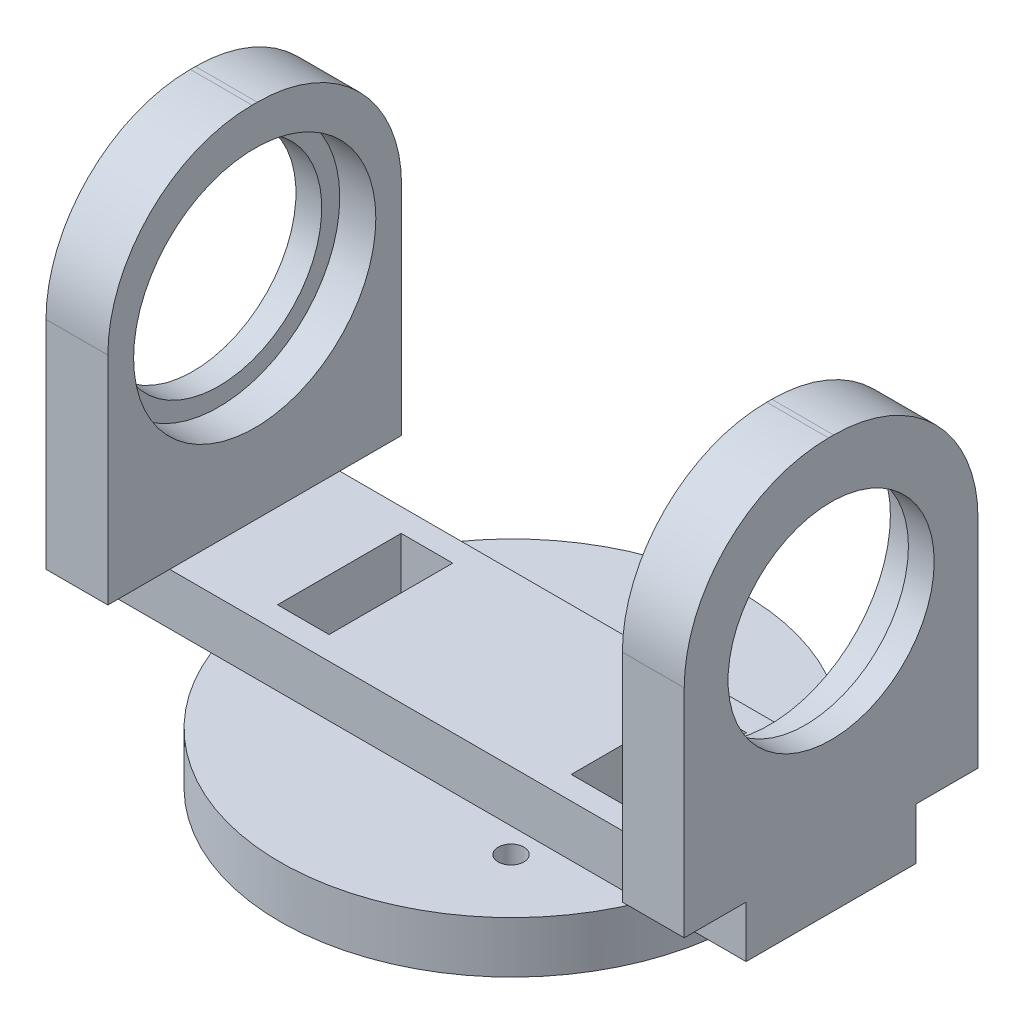
SolidWorks part; units mm, degrees
ref_plane "Front Plane" through (0, 0, 0) normal (0, 0, 1) x (1, 0, 0)
ref_plane "Top Plane" through (0, 0, 0) normal (0, 1, 0) x (1, 0, 0)
ref_plane "Right Plane" through (0, 0, 0) normal (1, 0, 0) x (0, 0, -1)
sketch "Sketch1" plane through (0, 0, 0) normal (0, 1, 0) x (1, 0, 0)
  line L1 (-61.92, 16.5) -> (61.92, 16.5)
  line L2 (-61.92, 16.5) -> (-61.92, -16.5)
  line L3 (-61.92, -16.5) -> (61.92, -16.5)
  line L4 (61.92, 16.5) -> (61.92, -16.5)
  point P4 (-61.92, 0)
  point P6 (0, 16.5)
  dimension "D1" = 33
  dimension "D2" = 123.84
extrude "Boss-Extrude1" add sketch "Sketch1" along normal blind 10 contours L1 L4 L3 L2
sketch "Sketch2" plane through (0, 10, 0) normal (0, 1, 0) x (1, 0, 0)
  line L1 (-61.92, 28.5) -> (-49.92, 28.5)
  line L2 (-61.92, 28.5) -> (-61.92, -28.5)
  line L3 (-61.92, -28.5) -> (-49.92, -28.5)
  line L4 (-49.92, 28.5) -> (-49.92, -28.5)
  line L5 (-23.5, 7.472) -> (-23.5, -3.0599) construction
  line L10 (-61.92, 16.5) -> (-61.92, -16.5) construction
  line L11 (0, 0) -> (0, 32.5393) construction
  line L12 (49.92, 28.5) -> (49.92, -28.5)
  line L13 (61.92, -28.5) -> (49.92, -28.5)
  line L14 (61.92, 28.5) -> (61.92, -28.5)
  line L15 (61.92, 28.5) -> (49.92, 28.5)
  point P19 (-61.92, 0)
  point P21 (-61.92, 0)
  dimension "D1" = 26.42
  dimension "D2" = 23.5
  dimension "D3" = 57
extrude "Boss-Extrude2" add sketch "Sketch2" along normal blind 70
sketch "Sketch3" plane through (61.92, 0, 0) normal (1, 0, 0) x (0, 0, -1)
  line L6 (16.5, 0) -> (-16.5, 0) construction
  circle A0 centre (0, 49) radius 23.5
  dimension "47" = 47
  dimension "D2" = 49
extrude "Cut-Extrude1" cut sketch "Sketch3" against normal through all
sketch "Sketch10" plane through (0, 0, 0) normal (0, -1, 0) x (1, 0, 0)
  circle A0 centre (0, 0) radius 45
  dimension "90" = 90
extrude "Boss-Extrude5" add sketch "Sketch10" along normal blind 10
sketch "Sketch9" plane through (0, 10, 0) normal (0, 1, 0) x (1, 0, 0)
  line L1 (-33.5, 12) -> (-23.5, 12)
  line L2 (-33.5, 12) -> (-33.5, -12)
  line L3 (-33.5, -12) -> (-23.5, -12)
  line L4 (-23.5, 12) -> (-23.5, -12)
  line L6 (0, 0) -> (0, 22.2113) construction
  line L7 (23.5, 12) -> (23.5, -12)
  line L8 (33.5, -12) -> (23.5, -12)
  line L9 (33.5, 12) -> (33.5, -12)
  line L10 (33.5, 12) -> (23.5, 12)
  circle A0 centre (0, 0) radius 30 construction
  circle A1 centre (21.1187, -21.3073) radius 2.5
  circle A4 centre (21.3073, 21.1187) radius 2.5
  circle A5 centre (-21.1187, 21.3073) radius 2.5
  point P8 (-23.5, 0)
  dimension "D3" = 60
  dimension "D4" = 5
  dimension "D5" = 5
  dimension "D7" = 5
  dimension "D1" = 24
  dimension "D2" = 10
  dimension "D6" = 90
  dimension "D8" = 90
  dimension "D9" = 47
  dimension "D10" = 10
  dimension "D11" = 24
  dimension "D12" = 23.5
extrude "Cut-Extrude3" cut sketch "Sketch9" against normal through all
fillet "Fillet1" radius 28 4 edges at (-55.92, 80, -28.5) (-55.92, 80, 28.5) (55.92, 80, -28.5) (55.92, 80, 28.5)
sketch "Sketch11" plane through (61.92, 0, 0) normal (1, 0, 0) x (0, 0, -1)
  circle A0 centre (0, 49) radius 23.5
  circle A1 centre (0, 49) radius 20
  circle A2 centre (0, 49) radius 23.5 construction
  dimension "D1" = 40
extrude "Boss-Extrude6" add sketch "Sketch11" against normal blind 5
sketch "Sketch12" plane through (-61.92, 0, 0) normal (-1, 0, 0) x (0, 0, 1)
  circle A0 centre (0, 49) radius 23.5
  circle A1 centre (0, 49) radius 20
  circle A2 centre (0, 49) radius 23.5 construction
  dimension "D1" = 40
extrude "Boss-Extrude7" add sketch "Sketch12" against normal blind 5
